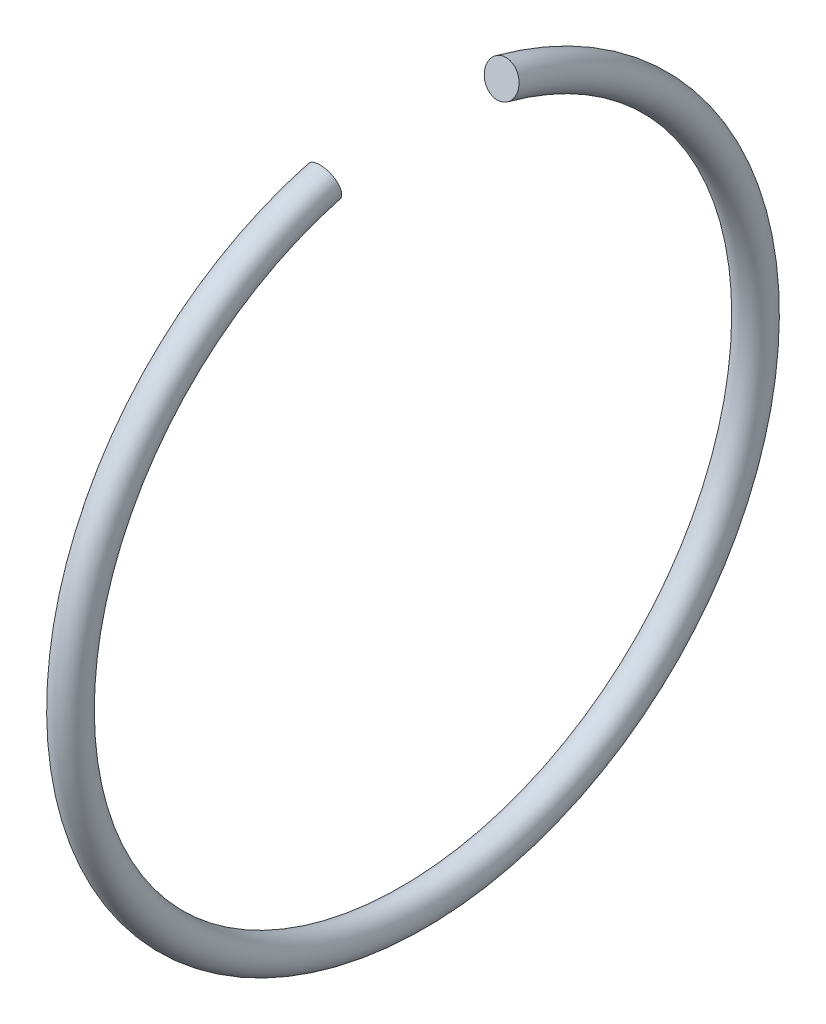
SolidWorks part; units mm, degrees
material "1.5714 (16NiCr4)"
ref_plane "Přední rovina" through (0, 0, 0) normal (0, 0, 1) x (1, 0, 0)
ref_plane "Horní rovina" through (0, 0, 0) normal (0, 1, 0) x (1, 0, 0)
ref_plane "Pravá rovina" through (0, 0, 0) normal (1, 0, 0) x (0, 0, -1)
sketch "Skica1" plane through (0, 0, 0) normal (0, 0, 1) x (1, 0, 0)
  line L0 (-67.4823, 0) -> (-363.0393, 0) construction
  line L1 (-67.4823, 0) -> (-363.0393, 0) construction
  circle A0 centre (-113.45, -32.5) radius 1.6 construction
  circle A1 centre (-113.45, -32.5) radius 1.6
revolve "Rotovat1" add sketch "Skica1" angle 330 mid plane about L1
